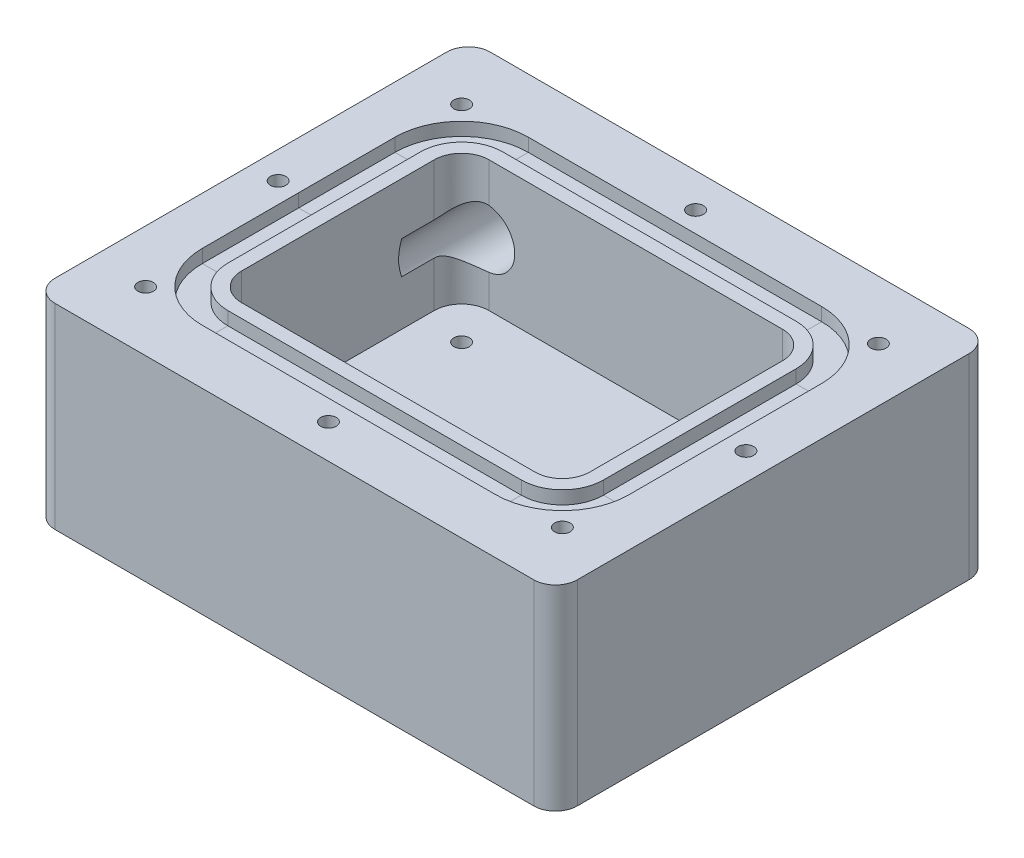
SolidWorks part; units mm, degrees
ref_plane "Front Plane" through (0, 0, 0) normal (0, 0, 1) x (1, 0, 0)
ref_plane "Top Plane" through (0, 0, 0) normal (0, 1, 0) x (1, 0, 0)
ref_plane "Right Plane" through (0, 0, 0) normal (1, 0, 0) x (0, 0, -1)
sketch "Sketch1" plane through (0, 0, 0) normal (0, 1, 0) x (1, 0, 0)
  line L1 (-38.1, 31.75) -> (38.1, 31.75)
  line L2 (-38.1, 31.75) -> (-38.1, -31.75)
  line L3 (-38.1, -31.75) -> (38.1, -31.75)
  line L4 (38.1, 31.75) -> (38.1, -31.75)
  line L5 (-38.1, 31.75) -> (38.1, -31.75) construction
  line L6 (-38.1, -31.75) -> (38.1, 31.75) construction
  point P0 (0, 0)
  dimension "D1" = 63.5
  dimension "D2" = 76.2
extrude "Boss-Extrude1" add sketch "Sketch1" along normal mid plane 28.575
sketch "Sketch2" plane through (0, 14.2875, 0) normal (0, 1, 0) x (1, 0, 0)
  line L0 (-25.4, 0) -> (-38.1, 0) construction
  line L1 (-25.4, 18.05) -> (25.4, 18.05)
  line L2 (-25.4, 18.05) -> (-25.4, -18.05)
  line L3 (-25.4, -18.05) -> (25.4, -18.05)
  line L4 (25.4, 18.05) -> (25.4, -18.05)
  line L5 (-25.4, 18.05) -> (25.4, -18.05) construction
  line L6 (-25.4, -18.05) -> (25.4, 18.05) construction
  line L7 (-38.1, 31.75) -> (-38.1, -31.75) construction
  line L8 (0, 18.05) -> (0, 31.75) construction
  line L9 (38.1, 31.75) -> (-38.1, 31.75) construction
  point P0 (0, 0)
  dimension "D1" = 12.7
  dimension "D2" = 13.7
extrude "Cut-Extrude1" cut sketch "Sketch2" against normal blind 19.05
sketch "Sketch10" plane through (0, 0, -31.75) normal (0, 0, -1) x (-1, 0, 0)
  line L1 (25.4, -4.7625) -> (25.4, 14.2875) construction
  line L2 (25.4, 4.2875) -> (21.9, 4.2875) construction
  line L3 (25.4, -4.7625) -> (25.4, 14.2875)
  line L4 (-38.1, 14.2875) -> (38.1, 14.2875) construction
  point P0 (19.2069, 5.0344)
  point P5 (21.9, 4.2875)
  dimension "D1" = 3.5
  dimension "D2" = 10
hole_wizard "M10x1.5 Tapped Hole1" positions "3DSketch3" profile "Sketch11" tap size "M10x1.5" standard "ANSI Metric"
sketch3d "3DSketch3"
  point P0 (-21.9, 4.2875, -31.75)
  point P7 (0, 0, 0)
sketch "Sketch11" plane through (-21.9, 4.2875, -31.75) normal (1, 0, 0) x (0, 1, 0)
  line L0 (0, 0) -> (0, 25)
  line L1 (0, 25) -> (4.25, 22.4463)
  line L2 (4.25, 22.4463) -> (4.25, 0)
  line L5 (4.25, 0) -> (0, 0)
  line L10 (0, 25) -> (-4.25, 22.4463) construction
  line L11 (0, -6.35) -> (0, 107.95) construction
  dimension "Tap Drill Dia." = 8.5
  dimension "Tap Drill Depth" = 25
  dimension "Drill Angle" = 118
cosmetic thread "Hole Thread7" parameters "D1"=20, "D2"=10
sketch "Sketch14" plane through (0, 14.2875, 0) normal (0, 1, 0) x (1, 0, 0)
  line L0 (0, 18.05) -> (0, 20.05) construction
  line L1 (-21.4, 20.05) -> (21.4, 20.05)
  line L2 (-27.4, 14.05) -> (-27.4, -14.05)
  line L3 (-21.4, -20.05) -> (21.4, -20.05)
  line L4 (27.4, 14.05) -> (27.4, -14.05)
  line L5 (25.4, 18.05) -> (-25.4, 18.05) construction
  line L6 (-27.4, 0) -> (-25.4, 0) construction
  line L7 (-25.4, 18.05) -> (-25.4, -18.05) construction
  line L8 (0, -20.05) -> (0, -18.05) construction
  line L9 (-25.4, -18.05) -> (25.4, -18.05) construction
  line L10 (25.4, 0) -> (27.4, 0) construction
  line L11 (25.4, -18.05) -> (25.4, 18.05) construction
  line L12 (-25.4, 14.875) -> (-25.4, -3.875) construction
  arc A0 (21.4, -20.05) -> (27.4, -14.05) centre (21.4, -14.05) ccw
  arc A1 (27.4, 14.05) -> (21.4, 20.05) centre (21.4, 14.05) ccw
  arc A2 (-21.4, -20.05) -> (-27.4, -14.05) centre (-21.4, -14.05) cw
  arc A3 (-21.4, 20.05) -> (-27.4, 14.05) centre (-21.4, 14.05) ccw
  point P24 (27.4, 20.05)
  point P27 (-27.4, -20.05)
  point P30 (-27.4, 20.05)
  dimension "RingPathRadius" = 6
  dimension "RingInnerLength" = 54.8
  dimension "RingInnerWidth" = 40.1
  dimension "ORingExtrusionGap" = 2
sketch "Sketch16" plane through (0, 0, 0) normal (0, 0, 1) x (1, 0, 0)
  line L1 (-27.4, 14.2875) -> (-31.1242, 14.2875)
  line L2 (-27.4, 14.2875) -> (-27.4, 12.3635)
  line L3 (-27.4, 12.3635) -> (-31.1242, 12.3635)
  line L4 (-31.1242, 14.2875) -> (-31.1242, 12.3635)
  dimension "GlandDepth" = 1.9241
  dimension "GlandWidth" = 3.7242
sweep "Cut-Sweep1" cut profiles "Sketch16" path "Sketch14"
fillet "Fillet2" radius 3.175 4 edges at (38.1, 0, 31.75) (-38.1, 0, 31.75) (-38.1, 0, -31.75) (38.1, 0, -31.75)
sketch "Sketch18" plane through (0, 14.2875, 0) normal (0, 1, 0) x (1, 0, 0)
  line L35 (-21.4, 26.7742) -> (-21.4, 23.7742) construction
  line L36 (-21.4, 26.7742) -> (-21.4, 31.75) construction
  line L37 (34.925, 31.75) -> (-34.925, 31.75) construction
  line L38 (-21.4, -23.7742) -> (-21.4, -26.7742) construction
  line L39 (-34.1242, 0) -> (-38.1, 0) construction
  line L40 (-38.1, 28.575) -> (-38.1, -28.575) construction
  line L41 (-34.1242, 0) -> (-31.1242, 0) construction
  line L42 (-31.1242, 0) -> (31.1242, 0) construction
  line L43 (31.1242, 14.05) -> (31.1242, -14.05) construction
  line L44 (31.1242, 0) -> (34.1242, 0) construction
  line L45 (34.1242, -14.05) -> (34.1242, 14.55) construction
  line L46 (-21.4, -26.7742) -> (21.4, -26.7742) construction
  line L47 (-34.1242, 0) -> (-34.1242, -14.05) construction
  line L48 (-34.1242, 14.05) -> (-34.1242, 0) construction
  line L49 (21.4098, 26.7742) -> (-21.4, 26.7742) construction
  line L50 (34.1242, 0) -> (38.1, 0) construction
  line L51 (38.1, -28.575) -> (38.1, 28.575) construction
  line L52 (-31.1242, -14.05) -> (-31.1242, 0) construction
  arc A30 (34.1242, 14.55) -> (21.4098, 26.7742) centre (21.4098, 14.05) ccw construction
  arc A31 (21.4, -26.7742) -> (34.1242, -14.05) centre (21.4, -14.05) ccw construction
  arc A32 (-34.1242, -14.05) -> (-21.4, -26.7742) centre (-21.4, -14.05) ccw construction
  arc A33 (-21.4, 26.7742) -> (-34.1242, 14.05) centre (-21.4, 14.05) ccw construction
  point P13 (30.2287, 23.2225)
  point P17 (-30.3974, 23.0474)
  point P18 (30.3974, -23.0474)
  point P19 (-30.3974, -23.0474)
  point P20 (0, -26.7742)
  point P22 (-34.1242, 0)
  point P89 (0.0049, 26.7742)
  point P94 (34.1242, 0)
  dimension "D1" = 3
hole_wizard "#4-40 Tapped Hole2" positions "Sketch18" profile "Sketch19" tap size "#4-40" standard "ANSI Inch"
sketch "Sketch19" plane through (34.1242, 14.2875, 0) normal (1, 0, 0) x (0, 0, 1)
  line L0 (0, 0) -> (0, 7.6)
  line L1 (0, 7.6) -> (1.1303, 6.9208)
  line L2 (1.1303, 6.9208) -> (1.1303, 0)
  line L5 (1.1303, 0) -> (0, 0)
  line L10 (0, 7.6) -> (-1.1303, 6.9208) construction
  line L11 (0, -6.35) -> (0, 107.95) construction
  dimension "Tap Drill Dia." = 2.2606
  dimension "Tap Drill Depth" = 7.6
  dimension "Drill Angle" = 118
cosmetic thread "Hole Thread9" parameters "D1"=5.69, "D2"=2.8448
cosmetic thread "Hole Thread10" parameters "D1"=5.69, "D2"=2.8448
cosmetic thread "Hole Thread11" parameters "D1"=5.69, "D2"=2.8448
cosmetic thread "Hole Thread12" parameters "D1"=5.69, "D2"=2.8448
cosmetic thread "Hole Thread13" parameters "D1"=5.69, "D2"=2.8448
cosmetic thread "Hole Thread14" parameters "D1"=5.69, "D2"=2.8448
cosmetic thread "Hole Thread15" parameters "D1"=5.69, "D2"=2.8448
cosmetic thread "Hole Thread16" parameters "D1"=5.69, "D2"=2.8448
fillet "Fillet3" radius 4 5 edges at (-25.4, 4.7625, 18.05) (-25.4, 10.493, -18.05) (-25.4, -1.443, -18.05) (25.4, 4.7625, -18.05) (25.4, 4.7625, 18.05)
sketch "Sketch20" plane through (0, -4.7625, 0) normal (0, 1, 0) x (1, 0, 0)
  line L0 (-25.4, 12.05) -> (-19.4, 12.05) construction
  line L3 (-25.4, 14.05) -> (-25.4, -14.05) construction
  line L4 (-19.4, 12.05) -> (19.4, 12.05) construction
  line L5 (19.4, 12.05) -> (25.4, 12.05) construction
  line L6 (25.4, -14.05) -> (25.4, 14.05) construction
  line L7 (-25.4, -12.05) -> (-19.4, -12.05) construction
  line L8 (-25.4, 14.05) -> (-25.4, -14.05) construction
  line L9 (-19.4, -12.05) -> (19.4, -12.05) construction
  line L10 (19.4, -12.05) -> (25.4, -12.05) construction
  line L11 (25.4, -14.05) -> (25.4, 14.05) construction
  line L12 (-19.4, 12.05) -> (-19.4, 18.05) construction
  line L13 (21.4, 18.05) -> (-21.4, 18.05) construction
  line L14 (-19.4, -12.05) -> (-19.4, -18.05) construction
  line L15 (-21.4, -18.05) -> (21.4, -18.05) construction
  point P23 (-19.4, 12.05)
  point P24 (19.4, 12.05)
  point P25 (19.4, -12.05)
  point P26 (-19.4, -12.05)
  dimension "D1" = 6
hole_wizard "#4-40 Tapped Hole3" positions "3DSketch4" profile "Sketch21" tap size "#4-40" standard "ANSI Inch"
sketch3d "3DSketch4"
  point P0 (19.4, -4.7625, -12.05)
  point P3 (19.4, -4.7625, 12.05)
  point P6 (-19.4, -4.7625, 12.05)
  point P9 (-19.4, -4.7625, -12.05)
sketch "Sketch21" plane through (19.4, -4.7625, -12.05) normal (1, 0, 0) x (0, 0, 1)
  line L0 (0, 0) -> (0, 5)
  line L1 (0, 5) -> (1.1303, 4.3208)
  line L2 (1.1303, 4.3208) -> (1.1303, 0)
  line L5 (1.1303, 0) -> (0, 0)
  line L10 (0, 5) -> (-1.1303, 4.3208) construction
  line L11 (0, -6.35) -> (0, 107.95) construction
  dimension "Tap Drill Dia." = 2.2606
  dimension "Tap Drill Depth" = 5
  dimension "Drill Angle" = 118
cosmetic thread "Hole Thread17" parameters "D1"=5.69, "D2"=2.8448
cosmetic thread "Hole Thread18" parameters "D1"=5.69, "D2"=2.8448
cosmetic thread "Hole Thread19" parameters "D1"=5.69, "D2"=2.8448
cosmetic thread "Hole Thread20" parameters "D1"=5.69, "D2"=2.8448
sketch "Sketch22" plane through (0, -14.2875, 0) normal (0, -1, 0) x (1, 0, 0)
  line L0 (-26.15, -31.75) -> (-17.65, -31.75) construction
  line L1 (-27.4, -12.7) -> (-38.1, -12.7) construction
  line L2 (-27.4, 12.7) -> (-38.1, 12.7) construction
  line L3 (-26.15, -31.75) -> (-17.65, -31.75) construction
  line L4 (-26.15, -31.75) -> (-26.15, -17.7157) construction
  line L5 (-17.65, -31.75) -> (-17.65, -20.05) construction
  line L6 (27.4, 12.7) -> (38.1, 12.7) construction
  line L7 (27.4, -12.7) -> (38.1, -12.7) construction
  line L8 (38.1, -28.575) -> (38.1, 28.575)
  line L9 (-27.4, 0) -> (-27.4, -14.05)
  line L10 (-27.4, 14.05) -> (-27.4, 0)
  line L11 (21.4, 20.05) -> (-21.4, 20.05)
  line L12 (27.4, -14.05) -> (27.4, 14.05)
  line L13 (-21.4, -20.05) -> (21.4, -20.05)
  line L14 (-27.4, 0) -> (-27.4, -14.05) construction
  line L15 (-27.4, 14.05) -> (-27.4, 0) construction
  line L16 (21.4, 20.05) -> (-21.4, 20.05) construction
  line L17 (27.4, -14.05) -> (27.4, 14.05) construction
  line L18 (-21.4, -20.05) -> (21.4, -20.05) construction
  line L19 (-34.925, -31.75) -> (34.925, -31.75)
  line L20 (-38.1, 28.575) -> (-38.1, -28.575)
  line L21 (34.925, 31.75) -> (-34.925, 31.75)
  line L22 (38.1, -28.575) -> (38.1, 28.575) construction
  line L23 (-34.925, -31.75) -> (34.925, -31.75) construction
  line L24 (-38.1, 28.575) -> (-38.1, -28.575) construction
  line L25 (34.925, 31.75) -> (-34.925, 31.75) construction
  line L26 (38.1, -12.7) -> (34.925, -31.75) construction
  line L27 (38.1, 12.7) -> (34.925, 31.75) construction
  arc A4 (-27.4, -14.05) -> (-21.4, -20.05) centre (-21.4, -14.05) ccw
  arc A5 (-21.4, 20.05) -> (-27.4, 14.05) centre (-21.4, 14.05) ccw
  arc A6 (27.4, 14.05) -> (21.4, 20.05) centre (21.4, 14.05) ccw
  arc A7 (21.4, -20.05) -> (27.4, -14.05) centre (21.4, -14.05) ccw
  arc A8 (-27.4, -14.05) -> (-21.4, -20.05) centre (-21.4, -14.05) ccw construction
  arc A9 (-21.4, 20.05) -> (-27.4, 14.05) centre (-21.4, 14.05) ccw construction
  arc A10 (27.4, 14.05) -> (21.4, 20.05) centre (21.4, 14.05) ccw construction
  arc A11 (21.4, -20.05) -> (27.4, -14.05) centre (21.4, -14.05) ccw construction
  arc A12 (34.925, -31.75) -> (38.1, -28.575) centre (34.925, -28.575) ccw
  arc A13 (-38.1, -28.575) -> (-34.925, -31.75) centre (-34.925, -28.575) ccw
  arc A14 (-34.925, 31.75) -> (-38.1, 28.575) centre (-34.925, 28.575) ccw
  arc A15 (38.1, 28.575) -> (34.925, 31.75) centre (34.925, 28.575) ccw
  arc A16 (34.925, -31.75) -> (38.1, -28.575) centre (34.925, -28.575) ccw construction
  arc A17 (-38.1, -28.575) -> (-34.925, -31.75) centre (-34.925, -28.575) ccw construction
  arc A18 (-34.925, 31.75) -> (-38.1, 28.575) centre (-34.925, 28.575) ccw construction
  arc A19 (38.1, 28.575) -> (34.925, 31.75) centre (34.925, 28.575) ccw construction
  point P37 (-32.75, 12.7)
  point P38 (-32.75, -12.7)
  point P39 (32.75, 12.7)
  point P40 (32.75, -12.7)
  point P41 (0, 0)
  dimension "D3" = 25.4
  dimension "D1" = 0
  dimension "D2" = 0
hole_wizard "#8-32 Tapped Hole1" positions "Sketch22" profile "Sketch23" tap size "#8-32" standard "ANSI Inch"
sketch "Sketch23" plane through (32.75, -14.2875, -12.7) normal (1, 0, 0) x (0, 0, -1)
  line L0 (0, 0) -> (0, 10.71)
  line L1 (0, 10.71) -> (1.7272, 9.6722)
  line L2 (1.7272, 9.6722) -> (1.7272, 0)
  line L5 (1.7272, 0) -> (0, 0)
  line L10 (0, 10.71) -> (-1.7272, 9.6722) construction
  line L11 (0, -6.35) -> (0, 107.95) construction
  dimension "Tap Drill Dia." = 3.4544
  dimension "Tap Drill Depth" = 10.71
  dimension "Drill Angle" = 118
cosmetic thread "Hole Thread21" parameters "D1"=8.33, "D2"=4.1656
cosmetic thread "Hole Thread22" parameters "D1"=8.33, "D2"=4.1656
cosmetic thread "Hole Thread23" parameters "D1"=8.33, "D2"=4.1656
cosmetic thread "Hole Thread24" parameters "D1"=8.33, "D2"=4.1656
equation "\"InnerRingWidth\"= 40.1'mm"
equation "\"InnerRingLength\"= 54.8'mm"
equation "\"RingPathRadius\"= 6'mm"
equation "\"RingPathLength\"= 2 * \"InnerRingLength\" + 2 * \"InnerRingWidth\" - ( 8 - 2 * 3.1415 ) * \"RingPathRadius\"'mm"
equation "\"RingStretch\"= .03"
equation "\"RingNomInnerDiameter\"= \"RingPathLength\" / 3.1415 / ( 1 + \"RingStretch\" ) / 25.4'Inches"
equation "\"RingInnerLength@Sketch14\"= \"InnerRingLength\""
equation "\"RingInnerWidth@Sketch14\"= \"InnerRingWidth\""
equation "\"RingPathRadius@Sketch14\"= \"RingPathRadius\""
equation "\"RingCompression\"= .25"
equation "\"RingCrossSectionHeight\"= .101'In"
equation "\"GlandDepth\"= \"RingCrossSectionHeight\" * ( 1 - \"RingCompression\" )'In"
equation "\"CrossSectionArea\"= .00833'In^2"
equation "\"GlandWidth\"= \"CrossSectionArea\" / \"GlandDepth\" / ( \"GlandFill\" )'In"
equation "\"GlandFill\"= .75"
equation "\"GlandWidth@Sketch16\"= \"GlandWidth\" * 25.4"
equation "\"GlandDepth@Sketch16\"= \"GlandDepth\" * 25.4"
